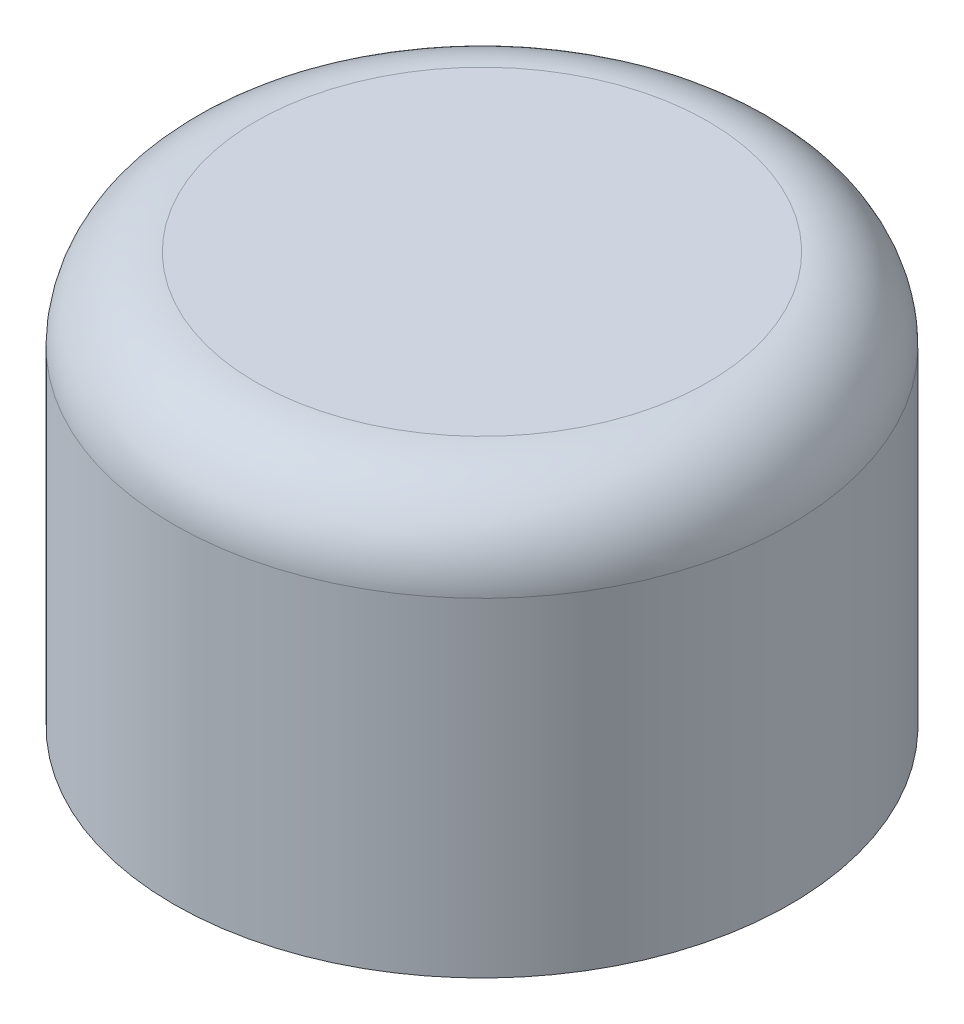
SolidWorks part; units mm, degrees
material "1060 Alloy"
ref_plane "Front Plane" through (0, 0, 0) normal (0, 0, 1) x (1, 0, 0)
ref_plane "Top Plane" through (0, 0, 0) normal (0, 1, 0) x (1, 0, 0)
ref_plane "Right Plane" through (0, 0, 0) normal (1, 0, 0) x (0, 0, -1)
sketch "Sketch2" plane through (0, 0, 0) normal (0, 1, 0) x (1, 0, 0)
  circle A0 centre (0, 0) radius 15
  dimension "D1" = 30
extrude "Boss-Extrude1" add sketch "Sketch2" along normal blind 20
hole_wizard "Tap Drill for M18x2.5 Tap1" positions "Sketch3" profile "Sketch4" hole size "M18x2.5" standard "ANSI Metric"
sketch "Sketch3" plane through (0, 0, 0) normal (0, -1, 0) x (-1, 0, 0)
  point P0 (0, 0)
sketch "Sketch4" plane through (0, 0, 0) normal (1, 0, 0) x (0, 0, -1)
  line L0 (0, 0) -> (0, 19.6567)
  line L1 (0, 19.6567) -> (7.75, 15)
  line L2 (7.75, 15) -> (7.75, 0)
  line L5 (7.75, 0) -> (0, 0)
  line L10 (0, 19.6567) -> (-7.75, 15) construction
  line L11 (0, -6.35) -> (0, 107.95) construction
  dimension "Hole Dia." = 15.5
  dimension "Hole Depth" = 15
  dimension "Drill Angle" = 118
fillet "Fillet1" radius 4 1 edges at (0, 20, 15)
equation "\"tubeOutDiameter\" = 35mm"
equation "\"wheelShaftDiameter\"= 12mm"
equation "\"wheelThickness\"= 135mm"
equation "\"BearingDiameter\"= 20mm"
equation "\"BearingThickness\"= 10mm"
equation "\"frontShaftDiameter\"= 20mm"
equation "\"D1@Sketch2\"= \"frontShaftDiameter\" * 1.5"
